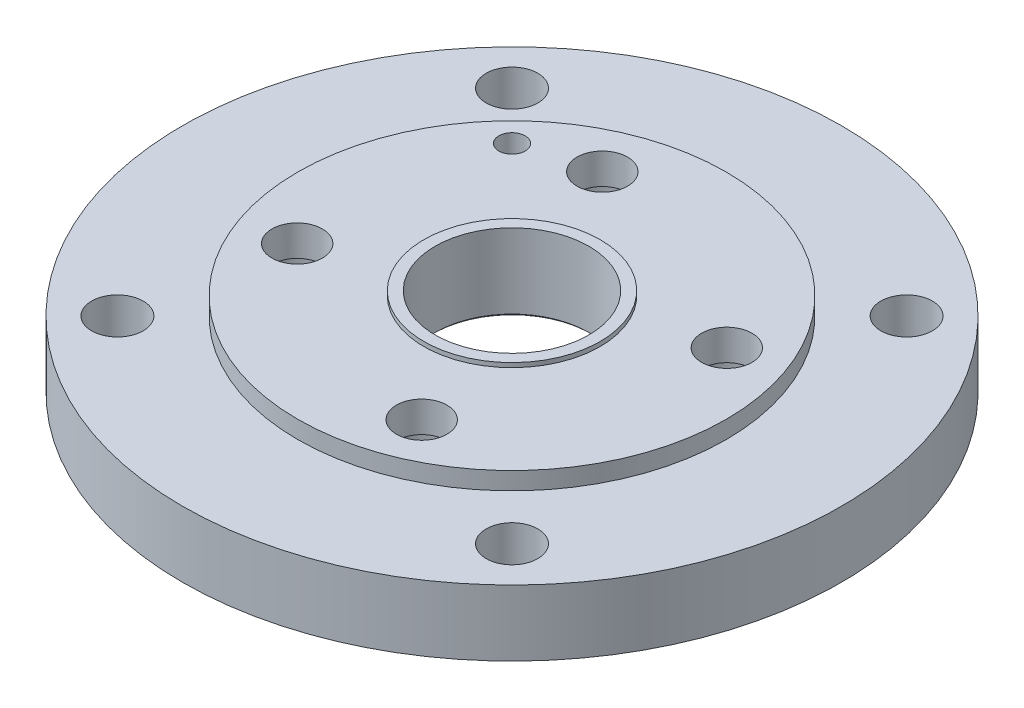
SolidWorks part; units mm, degrees
ref_plane "정면" through (0, 0, 0) normal (0, 0, 1) x (1, 0, 0)
ref_plane "평면" through (0, 0, 0) normal (0, 1, 0) x (1, 0, 0)
ref_plane "우측면" through (0, 0, 0) normal (1, 0, 0) x (0, 0, -1)
sketch "스케치1" plane through (0, 0, 0) normal (0, 0, 1) x (1, 0, 0)
  line L1 (-150, 0) -> (-150, 30)
  line L2 (-40.15, 40) -> (-35, 40)
  line L4 (0, 0) -> (0, 40) construction
  line L5 (-97.5, 0) -> (-97.5, 40) construction
  line L6 (-35, 5) -> (-35, 40)
  line L7 (-97.5, 30) -> (-150, 30)
  line L8 (-43.5, 0) -> (-43.5, 5)
  line L10 (-40.15, 38) -> (-40.15, 40)
  line L11 (-40.15, 0) -> (-40.15, 40) construction
  line L12 (-43.5, 0) -> (-43.5, 40) construction
  line L13 (-35, 0) -> (-35, 40) construction
  line L15 (-35, 5) -> (-43.5, 5)
  line L19 (-97.5, 30) -> (-97.5, 38)
  line L24 (-40.15, 38) -> (-97.5, 38)
  line L27 (-43.5, 0) -> (-150, 0)
  dimension "D1" = 43.5
  dimension "D2" = 35
  dimension "D3" = 5
  dimension "D4" = 40
  dimension "D5" = 150
  dimension "D6" = 97.5
  dimension "D7" = 30
  dimension "D8" = 38
  dimension "D9" = 40
  dimension "D10" = 40.15
revolve "회전1" add sketch "스케치1" angle 360 about L4
chamfer "모따기1" distance 1 angle 45 2 edges at (0, 0, -43.5) (0, 5, -35)
sketch "스케치2" plane through (0, 0, 0) normal (0, 1, 0) x (1, 0, 0)
  line L0 (89.8026, -89.8026) -> (-89.8026, 89.8026) construction
  line L1 (0, 0) -> (-60, 0) construction
  line L2 (-89.8026, -89.8026) -> (89.8026, 89.8026) construction
  line L3 (-60, 0) -> (-60, 60) construction
  circle A0 centre (0, 0) radius 127 construction
  circle A1 centre (-60, 60) radius 6
  circle A2 centre (-89.8026, 89.8026) radius 11.75
  circle A3 centre (89.8026, 89.8026) radius 11.75
  circle A4 centre (89.8026, -89.8026) radius 11.75
  circle A5 centre (-89.8026, -89.8026) radius 11.75
  point P20 (0, 0)
  dimension "D1" = 254
  dimension "D2" = 60
  dimension "D4" = 12
  dimension "D5" = 4
  dimension "D6" = 23.5
  dimension "D3" = 60
extrude "컷-돌출1" cut sketch "스케치2" along normal up to next
sketch "스케치3" plane through (0, 0, 0) normal (0, 1, 0) x (1, 0, 0)
  line L0 (0, 0) -> (-28.3381, 69.4403) construction
  line L1 (0, 0) -> (0, 75) construction
  circle A0 centre (0, 0) radius 75 construction
  circle A1 centre (-28.3381, 69.4403) radius 11.5
  circle A2 centre (69.4403, 28.3381) radius 11.5
  circle A3 centre (28.3381, -69.4403) radius 11.5
  circle A4 centre (-69.4403, -28.3381) radius 11.5
  point P14 (0, 0)
  dimension "D1" = 23
  dimension "D2" = 150
  dimension "D4" = 22.2
  dimension "D3" = 4
extrude "컷-돌출2" cut sketch "스케치3" along normal up to next
sketch "스케치4" plane through (0, 0, 0) normal (0, 1, 0) x (1, 0, 0)
  circle A0 centre (-28.3381, 69.4403) radius 17.5
  circle A1 centre (-69.4403, -28.3381) radius 17.5
  circle A2 centre (69.4403, 28.3381) radius 17.5
  circle A3 centre (28.3381, -69.4403) radius 17.5
  dimension "D1" = 35
extrude "컷-돌출3" cut sketch "스케치4" along normal blind 24
